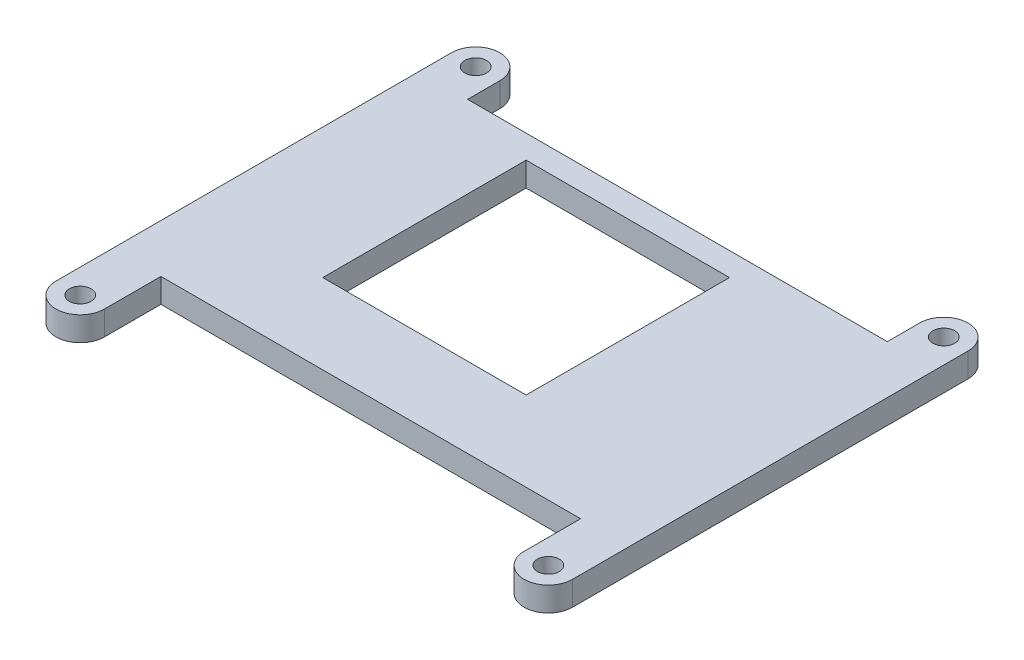
SolidWorks part; units mm, degrees
ref_plane "前视基准面" through (0, 0, 0) normal (0, 0, 1) x (1, 0, 0)
ref_plane "上视基准面" through (0, 0, 0) normal (0, 1, 0) x (1, 0, 0)
ref_plane "右视基准面" through (0, 0, 0) normal (1, 0, 0) x (0, 0, -1)
sketch "草图1" plane through (0, 0, 0) normal (0, 1, 0) x (1, 0, 0)
  line L0 (-12.6, 12.6) -> (12.6, -12.6) construction
  line L1 (-12.6, 12.6) -> (12.6, 12.6)
  line L2 (-12.6, 12.6) -> (-12.6, -12.6)
  line L3 (-12.6, -12.6) -> (12.6, -12.6)
  line L4 (12.6, 12.6) -> (12.6, -12.6)
  line L5 (-28.75, 19.5) -> (-28.75, -29.5)
  line L6 (35.25, 19.5) -> (35.25, -29.5)
  line L7 (-22.75, 15.5) -> (-22.75, 19.5)
  line L8 (-22.75, 15.5) -> (29.25, 15.5)
  line L9 (29.25, 15.5) -> (29.25, 19.5)
  line L10 (-22.75, -29.5) -> (-22.75, -22.5)
  line L11 (-22.75, -22.5) -> (29.25, -22.5)
  line L12 (29.25, -22.5) -> (29.25, -29.5)
  arc A0 (29.25, -29.5) -> (35.25, -29.5) centre (32.25, -29.5) ccw
  arc A1 (-28.75, -29.5) -> (-22.75, -29.5) centre (-25.75, -29.5) ccw
  arc A2 (35.25, 19.5) -> (29.25, 19.5) centre (32.25, 19.5) ccw
  arc A3 (-22.75, 19.5) -> (-28.75, 19.5) centre (-25.75, 19.5) ccw
  circle A4 centre (-25.75, 19.5) radius 1.35
  circle A5 centre (-25.75, -29.5) radius 1.35
  circle A6 centre (32.25, 19.5) radius 1.35
  circle A7 centre (32.25, -29.5) radius 1.35
  dimension "D8" = 55
  dimension "D9" = 7
  dimension "D11" = 2.7
  dimension "D1" = 25.2
  dimension "D2" = 16.15
  dimension "D3" = 64
  dimension "D4" = 22.5
  dimension "D5" = 6
  dimension "D6" = 6
  dimension "D7" = 10
  dimension "D10" = 25.2
extrude "凸台-拉伸1" add sketch "草图1" along normal blind 3
